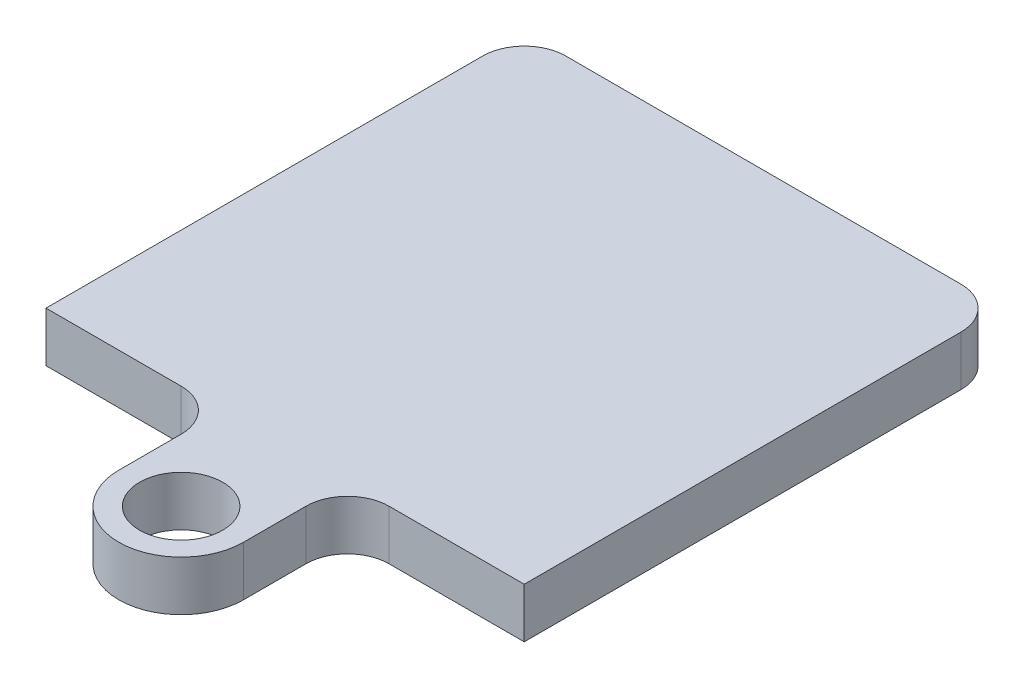
SolidWorks part; units mm, degrees
ref_plane "Front Plane" through (0, 0, 0) normal (0, 0, 1) x (1, 0, 0)
ref_plane "Top Plane" through (0, 0, 0) normal (0, 1, 0) x (1, 0, 0)
ref_plane "Right Plane" through (0, 0, 0) normal (1, 0, 0) x (0, 0, -1)
sketch "Sketch1" plane through (0, 0, 0) normal (0, 1, 0) x (1, 0, 0)
  line L1 (-11.5, 11.5) -> (11.5, 11.5)
  line L2 (-11.5, 11.5) -> (-11.5, -11.5)
  line L3 (-11.5, -11.5) -> (11.5, -11.5)
  line L4 (11.5, 11.5) -> (11.5, -11.5)
  dimension "D1" = 23
  dimension "D2" = 23
  dimension "D3" = 11.5
  dimension "D4" = 11.5
extrude "Boss-Extrude1" add sketch "Sketch1" along normal blind 2.4
fillet "Fillet1" radius 2 2 edges at (-11.5, 1.2, -11.5) (11.5, 1.2, -11.5)
sketch "Sketch2" plane through (0, 2.4, 0) normal (0, 1, 0) x (1, 0, 0)
  line L0 (-3, -11.5) -> (-3, -16.5)
  line L1 (-11.5, -11.5) -> (11.5, -11.5) construction
  line L2 (3, -16.5) -> (3, -11.5)
  line L3 (3, -11.5) -> (-3, -11.5)
  arc A0 (-3, -16.5) -> (3, -16.5) centre (0, -16.5) ccw
  circle A1 centre (0, -16.5) radius 2
  dimension "D1" = 3
  dimension "D4" = 4
  dimension "D2" = 5
  dimension "D3" = 3
extrude "Boss-Extrude2" add sketch "Sketch2" against normal up to surface (2.4 mm away) up to face at (0, 0, -3.3047)
fillet "Fillet2" radius 2 2 edges at (3, 1.2, 11.5) (-3, 1.2, 11.5)
